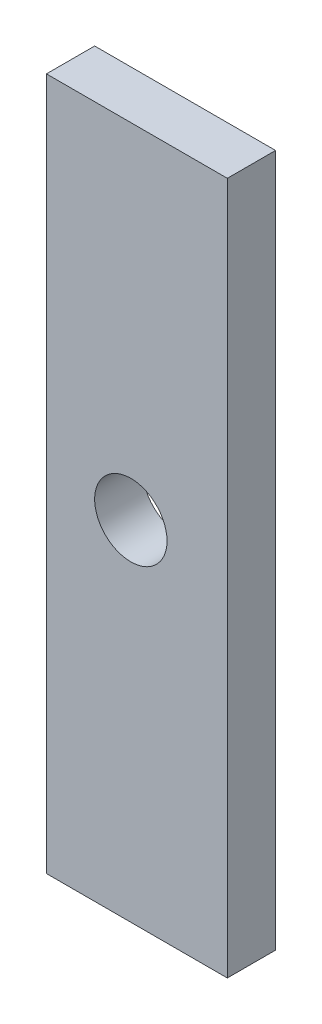
SolidWorks part; units mm, degrees
ref_plane "Front Plane" through (0, 0, 0) normal (0, 0, 1) x (1, 0, 0)
ref_plane "Top Plane" through (0, 0, 0) normal (0, 1, 0) x (1, 0, 0)
ref_plane "Right Plane" through (0, 0, 0) normal (1, 0, 0) x (0, 0, -1)
sketch "Sketch1" plane through (0, 0, 0) normal (0, 0, 1) x (1, 0, 0)
  line L0 (-3.5, 14.272) -> (4, 14.272)
  line L1 (-3.5, -14.441) -> (4, -14.441)
  line L2 (4, -14.441) -> (4, 14.272)
  line L3 (-3.5, 14.272) -> (-3.5, -14.441)
  circle A0 centre (0, 0) radius 1.5
  dimension "D1" = 3
  dimension "D2" = 4
  dimension "D3" = 3.5
  dimension "D4" = 14.272
  dimension "D5" = 14.441
extrude "Boss-Extrude1" add sketch "Sketch1" along normal blind 2
equation "\"D5@Sketch1\" = \"D76@Sketch1@palmUp<1>.Part\" - 6.72 - 0.41'Support Pully Thumb Palm Up"
